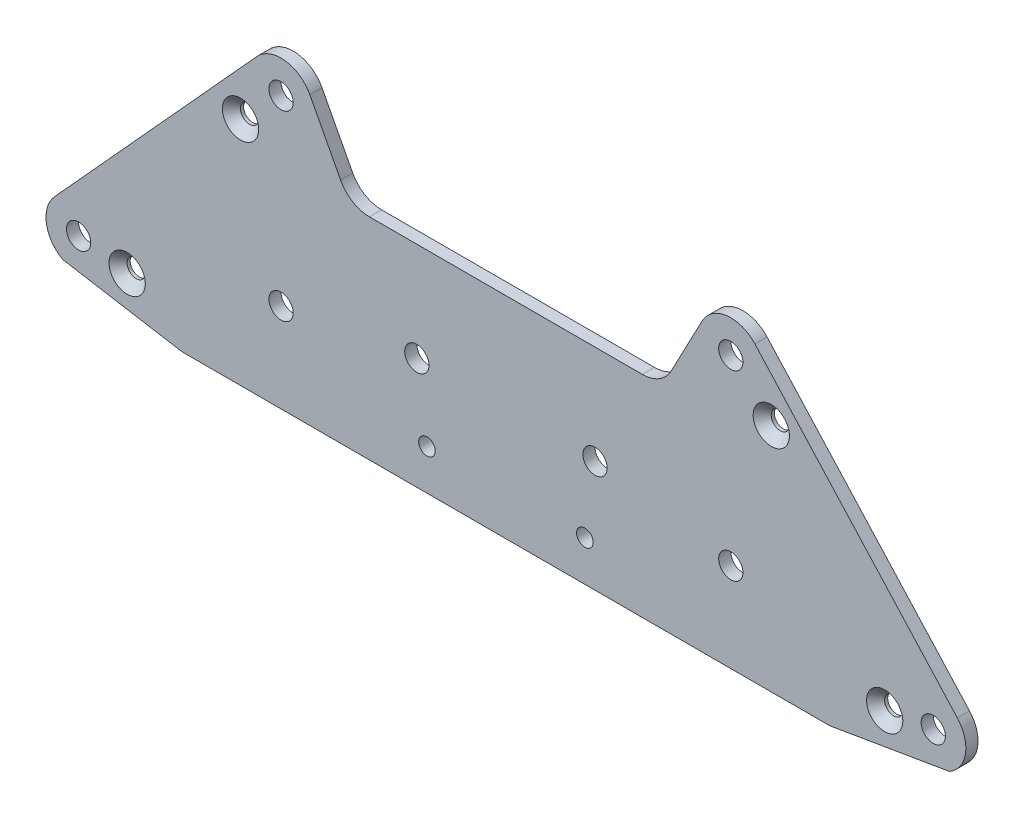
SolidWorks part; units mm, degrees
ref_plane "Front Plane" through (0, 0, 0) normal (0, 0, 1) x (1, 0, 0)
ref_plane "Top Plane" through (0, 0, 0) normal (0, 1, 0) x (1, 0, 0)
ref_plane "Right Plane" through (0, 0, 0) normal (1, 0, 0) x (0, 0, -1)
sketch "Sketch2" plane through (0, 0, 0) normal (0, 0, 1) x (1, 0, 0)
  line L0 (-80, -12) -> (80, -12)
  line L1 (-111.4901, 5.4124) -> (-61.4901, 60.4124)
  line L2 (-48.4142, 58.7434) -> (-40.8242, 44.3027)
  line L3 (-33.702, 40) -> (33.702, 40)
  line L4 (40.8242, 44.3027) -> (48.4142, 58.7434)
  line L5 (61.4901, 60.4124) -> (111.4901, 5.4124)
  line L6 (0, -30.3307) -> (0, 100.5226) construction
  line L7 (-128.998, 0) -> (134.7528, 0) construction
  line L8 (-80, -12) -> (-109.5038, -7)
  line L9 (80, -12) -> (109.5038, -7)
  arc A6 (-109.5038, -7) -> (-111.4901, 5.4124) centre (-105.5365, 0) cw
  arc A7 (-61.4901, 60.4124) -> (-48.4142, 58.7434) centre (-55.5365, 55) cw
  arc A8 (-40.8242, 44.3027) -> (-33.702, 40) centre (-33.702, 48.0461) ccw
  arc A9 (33.702, 40) -> (40.8242, 44.3027) centre (33.702, 48.0461) ccw
  arc A10 (48.4142, 58.7434) -> (61.4901, 60.4124) centre (55.5365, 55) cw
  arc A11 (111.4901, 5.4124) -> (109.5038, -7) centre (105.5365, 0) cw
  dimension "D2" = 12
  dimension "D3" = 40
  dimension "D4" = 80
  dimension "D10" = 70
  dimension "D5" = 5
  dimension "D6" = 80
  dimension "D7" = 5
  dimension "D11" = 70
extrude "Plate" add sketch "Sketch2" along normal blind 3
sketch "Sketch4" plane through (0, 0, 0) normal (0, 0, 1) x (1, 0, 0)
  line L0 (-55.5365, 69.6279) -> (-55.5365, -17.3447) construction
  line L1 (0, -30.3307) -> (0, 100.5226) construction
  line L2 (-80, -12) -> (80, -12) construction
  line L3 (55.5365, 69.6279) -> (55.5365, -17.3447) construction
  line L6 (0, -23.2032) -> (0, 75.274) construction
  circle A0 centre (105.5365, 0) radius 3
  circle A1 centre (55.5365, 10) radius 3
  circle A2 centre (55.5365, 55) radius 3
  circle A3 centre (-105.5365, 0) radius 3
  circle A4 centre (-55.5365, 10) radius 3
  circle A5 centre (-55.5365, 55) radius 3
  circle A6 centre (-21.9984, 15.5855) radius 3
  circle A7 centre (21.9984, 15.5855) radius 3
  point P19 (0, 27.4628)
  point P24 (0, -12)
  dimension "D1" = 6
  dimension "D2" = 10
  dimension "D3" = 25
  dimension "D4" = 25
  dimension "D9" = 21.9984
  dimension "D10" = 45
  dimension "D5" = 55.5365
  dimension "D6" = 10
  dimension "D7" = 55.5365
  dimension "D8" = 21.9984
  dimension "D11" = 45
extrude "Pivot holes (arm)" cut sketch "Sketch4" along normal through all
sketch "Sketch11" plane through (0, 0, 0) normal (0, 0, 1) x (1, 0, 0)
  line L6 (0, -25.9835) -> (0, 10.4229) construction
  circle A18 centre (0, 27.4628) radius 5
  dimension "D3" = 10
extrude "Inner plate drive hole" [suppressed] cut sketch "Sketch11" along normal through all
sketch "Sketch5" plane through (0, 0, 3) normal (0, 0, 1) x (1, 0, 0)
  line L0 (0, 49.0407) -> (0, -22.7774) construction
  line L1 (33.702, 40) -> (-33.702, 40) construction
  circle A0 centre (-105.5365, 0) radius 3 construction
  circle A4 centre (-19.5, -2) radius 2.05
  circle A5 centre (19.5, -2) radius 2.05
  point P4 (0, 40)
  dimension "D1" = 2
  dimension "D2" = 4.1
  dimension "D6" = 19.5
  dimension "D7" = 19.5
extrude "Chassis holes" cut sketch "Sketch5" against normal through all
hole_wizard "CSK for M4 SFHCS1" positions "Sketch8" profile "Sketch7" countersink size "M4" standard "Ansi Metric" end condition through all
sketch "Sketch8" plane through (26.9077, -2.1734, 3) normal (0, 0, -1) x (-1, 0, 0)
  circle A0 centre (132.4442, 2.1734) radius 3 construction
  point P0 (-66.6287, 0.1734)
  point P1 (-38.6287, 47.1734)
  point P4 (92.4442, 47.1734)
  point P6 (120.4442, 0.1734)
  dimension "D1" = 12
  dimension "D2" = 2
  dimension "D3" = 40
  dimension "D4" = 45
  dimension "D5" = 12
  dimension "D6" = 2
  dimension "D7" = 45
  dimension "D8" = 40
sketch "Sketch7" plane through (93.5365, -2, 3) normal (1, 0, 0) x (0, -1, 0)
  line L0 (0, 0) -> (0, 3)
  line L1 (0, 3) -> (2.25, 3)
  line L2 (2.25, 3) -> (2.25, 2.23)
  line L3 (2.25, 2.23) -> (4.48, 0)
  line L5 (4.48, 0) -> (0, 0)
  line L6 (-2.25, 2.23) -> (-4.48, 0) construction
  line L11 (0, -6.35) -> (0, 107.95) construction
  dimension "Thru Hole Dia." = 4.5
  dimension "Thru Hole Depth" = 3
  dimension "Near C'Sink Dia." = 8.96
  dimension "Near C'Sink Angle" = 90
